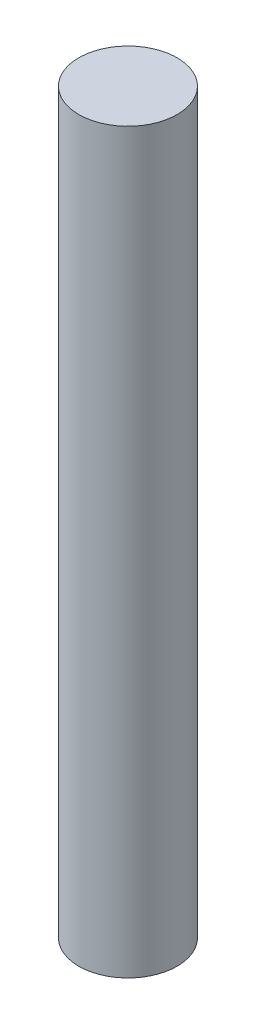
SolidWorks part; units mm, degrees
ref_plane "Front Plane" through (0, 0, 0) normal (0, 0, 1) x (1, 0, 0)
ref_plane "Top Plane" through (0, 0, 0) normal (0, 1, 0) x (1, 0, 0)
ref_plane "Right Plane" through (0, 0, 0) normal (1, 0, 0) x (0, 0, -1)
sketch "Sketch1" plane through (0, 0, 0) normal (0, 1, 0) x (1, 0, 0)
  circle A0 centre (0, 0) radius 1
  dimension "D1" = 2
extrude "Boss-Extrude1" add sketch "Sketch1" along normal blind 15
